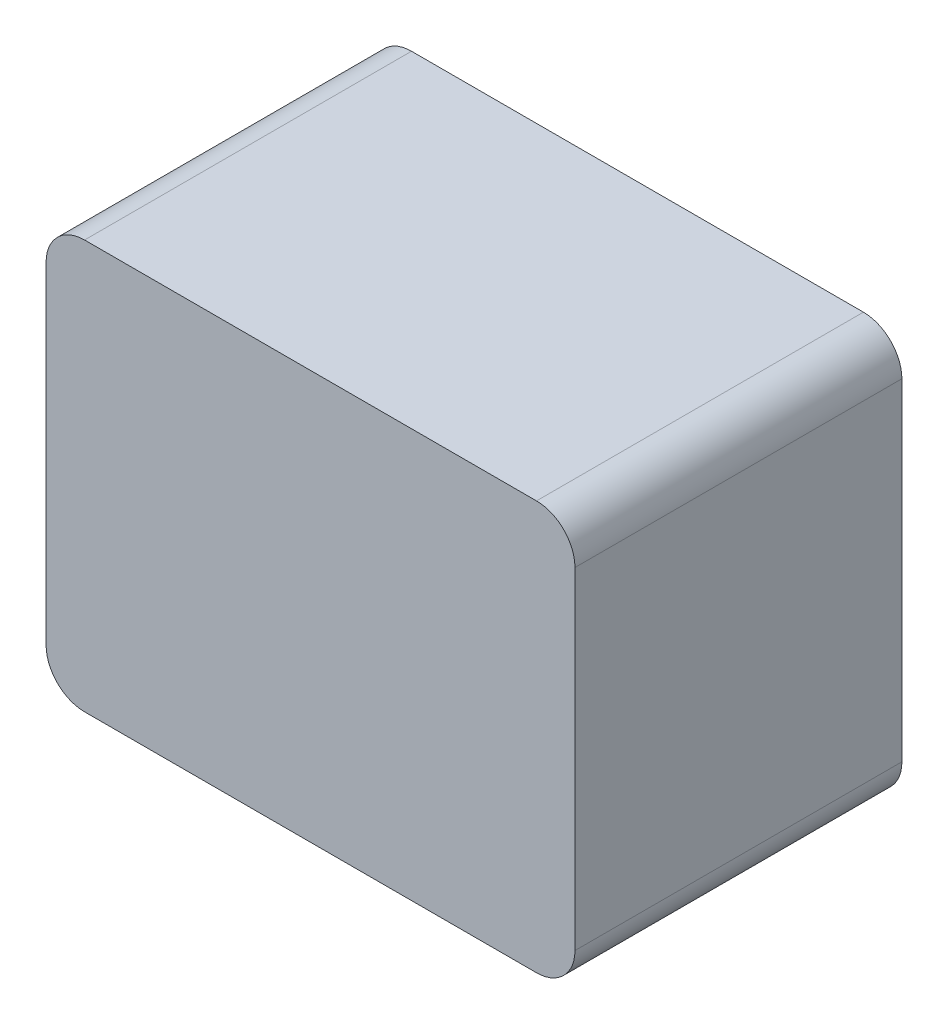
SolidWorks part; units mm, degrees
ref_plane "前视基准面" through (0, 0, 0) normal (0, 0, 1) x (1, 0, 0)
ref_plane "上视基准面" through (0, 0, 0) normal (0, 1, 0) x (1, 0, 0)
ref_plane "右视基准面" through (0, 0, 0) normal (1, 0, 0) x (0, 0, -1)
sketch "草图1" plane through (0, 0, 0) normal (0, 0, 1) x (1, 0, 0)
  line L1 (-95.212, 68.1171) -> (-1.212, 68.1171)
  line L2 (-103.212, 60.1171) -> (-103.212, -8.8829)
  line L3 (-95.212, -16.8829) -> (-1.212, -16.8829)
  line L4 (6.788, 60.1171) -> (6.788, -8.8829)
  line L5 (-103.212, 68.1171) -> (6.788, -16.8829) construction
  line L6 (-103.212, -16.8829) -> (6.788, 68.1171) construction
  arc A0 (-1.212, -16.8829) -> (6.788, -8.8829) centre (-1.212, -8.8829) ccw
  arc A1 (-103.212, -8.8829) -> (-95.212, -16.8829) centre (-95.212, -8.8829) ccw
  arc A2 (-95.212, 68.1171) -> (-103.212, 60.1171) centre (-95.212, 60.1171) ccw
  arc A3 (-1.212, 68.1171) -> (6.788, 60.1171) centre (-1.212, 60.1171) cw
  dimension "D3" = 8
  dimension "D1" = 110
  dimension "D2" = 85
extrude "凸台-拉伸1" add sketch "草图1" along normal blind 68
